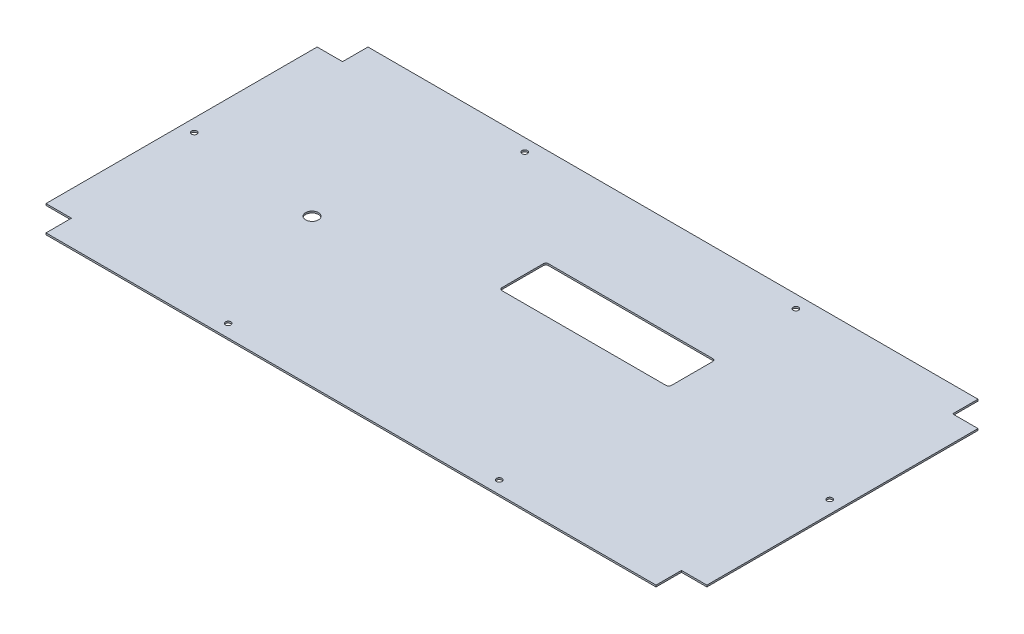
SolidWorks part; units mm, degrees
material "1.0037 (S235JR)"
ref_plane "Front Plane" through (0, 0, 0) normal (0, 0, 1) x (1, 0, 0)
ref_plane "Top Plane" through (0, 0, 0) normal (0, 1, 0) x (1, 0, 0)
ref_plane "Right Plane" through (0, 0, 0) normal (1, 0, 0) x (0, 0, -1)
sketch "Sketch2" plane through (0, 0, 0) normal (0, 1, 0) x (1, 0, 0)
  line L1 (-390, 190) -> (390, 190)
  line L2 (-390, 190) -> (-390, -190)
  line L3 (-390, -190) -> (390, -190)
  line L4 (390, 190) -> (390, -190)
  line L5 (-390, 190) -> (390, -190) construction
  line L6 (-390, -190) -> (390, 190) construction
  point P0 (0, 0)
  dimension "D1" = 780
  dimension "D2" = 380
extrude "Boss-Extrude1" add sketch "Sketch2" along normal blind 2
sketch "Sketch3" plane through (0, 2, 0) normal (0, 1, 0) x (1, 0, 0)
  line L1 (-390, 190) -> (-360, 190)
  line L2 (-390, 190) -> (-390, 160)
  line L3 (-390, 160) -> (-360, 160)
  line L4 (-360, 190) -> (-360, 160)
  line L5 (390, 190) -> (360, 190)
  line L6 (390, 190) -> (390, 160)
  line L7 (390, 160) -> (360, 160)
  line L8 (360, 190) -> (360, 160)
  line L9 (390, -190) -> (360, -190)
  line L10 (390, -190) -> (390, -160)
  line L11 (390, -160) -> (360, -160)
  line L12 (360, -190) -> (360, -160)
  line L13 (-390, -190) -> (-360, -190)
  line L14 (-390, -190) -> (-390, -160)
  line L15 (-390, -160) -> (-360, -160)
  line L16 (-360, -190) -> (-360, -160)
  dimension "D1" = 30
  dimension "D2" = 30
  dimension "D3" = 30
  dimension "D4" = 30
  dimension "D5" = 30
  dimension "D6" = 30
  dimension "D7" = 30
  dimension "D8" = 30
extrude "Cut-Extrude1" cut sketch "Sketch3" against normal through all
sketch "Sketch4" plane through (0, 2, 0) normal (0, 1, 0) x (1, 0, 0)
  line L0 (-390, 160) -> (-390, -160) construction
  line L1 (-360, -160) -> (-390, -160) construction
  line L2 (390, -160) -> (390, 160) construction
  line L3 (390, -160) -> (360, -160) construction
  line L4 (-360, 160) -> (-360, 190) construction
  line L5 (360, 190) -> (360, 160) construction
  line L6 (360, 190) -> (-360, 190) construction
  line L7 (-360, -190) -> (360, -190) construction
  line L8 (-360, -190) -> (-360, -160) construction
  line L9 (360, -160) -> (360, -190) construction
  circle A1 centre (-375, 0) radius 3.25
  circle A2 centre (375, 0) radius 3.25
  circle A3 centre (-160, 175) radius 3.25
  circle A4 centre (160, 175) radius 3.25
  circle A5 centre (-160, -175) radius 3.25
  circle A6 centre (160, -175) radius 3.25
  dimension "D2" = 6.5
  dimension "D5" = 6.5
  dimension "D7" = 6.5
  dimension "D1" = 15
  dimension "D3" = 160
  dimension "D4" = 15
  dimension "D6" = 160
  dimension "D8" = 200
  dimension "D9" = 200
  dimension "D10" = 15
  dimension "D11" = 15
  dimension "D12" = 15
  dimension "D13" = 200
  dimension "D14" = 15
  dimension "D15" = 200
extrude "Cut-Extrude2" cut sketch "Sketch4" against normal through all
sketch "Sketch5" plane through (0, 2, 0) normal (0, 1, 0) x (1, 0, 0)
  line L0 (-390, 160) -> (-390, -160) construction
  line L2 (0, 0) -> (-482.3923, 0) construction
  circle A0 centre (-220, -16) radius 7.5
  dimension "D1" = 15
  dimension "D2" = 170
  dimension "D3" = 16
extrude "Cut-Extrude3" cut sketch "Sketch5" against normal through all
sketch "Sketch6" plane through (0, 2, 0) normal (0, 1, 0) x (1, 0, 0)
  line L0 (-390, 160) -> (-390, -160) construction
  line L1 (-32, 75) -> (162, 75)
  line L2 (-35, 72) -> (-35, 23)
  line L3 (-32, 20) -> (162, 20)
  line L4 (165, 72) -> (165, 23)
  line L5 (360, 190) -> (-360, 190) construction
  arc A0 (162, 75) -> (165, 72) centre (162, 72) cw
  arc A1 (162, 20) -> (165, 23) centre (162, 23) ccw
  arc A2 (-35, 23) -> (-32, 20) centre (-32, 23) ccw
  arc A3 (-32, 75) -> (-35, 72) centre (-32, 72) ccw
  point P10 (165, 75)
  point P13 (165, 20)
  point P18 (-35, 75)
  dimension "D5" = 3
  dimension "D1" = 355
  dimension "D2" = 55
  dimension "D3" = 115
  dimension "D4" = 200
extrude "Cut-Extrude4" cut sketch "Sketch6" against normal through all
